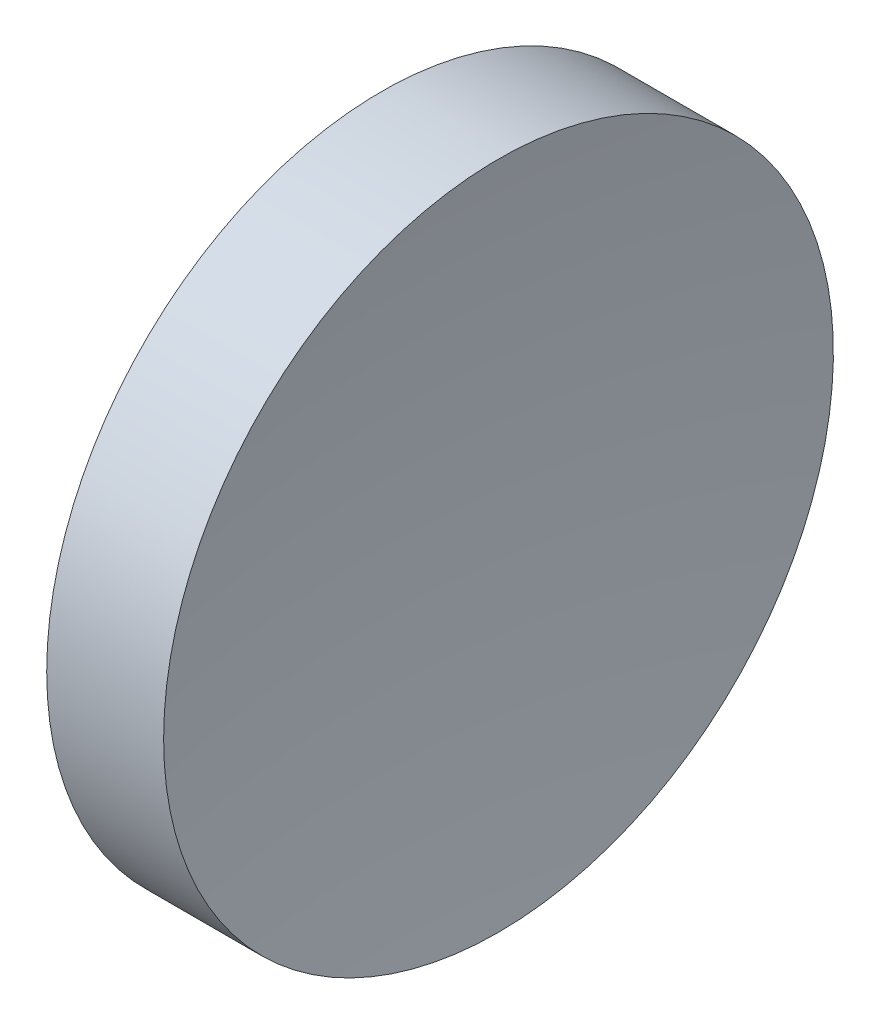
SolidWorks part; units mm, degrees
ref_plane "前视基准面" through (0, 0, 0) normal (0, 0, 1) x (1, 0, 0)
ref_plane "上视基准面" through (0, 0, 0) normal (0, 1, 0) x (1, 0, 0)
ref_plane "右视基准面" through (0, 0, 0) normal (1, 0, 0) x (0, 0, -1)
sketch "草图1" plane through (0, 0, 0) normal (0, 0, 1) x (1, 0, 0)
  line L0 (111.9552, 71.194) -> (137.836, 71.194) construction
  line L1 (119.5068, 71.194) -> (119.5068, 83.894)
  line L2 (119.5068, 83.894) -> (123.941, 83.894)
  line L3 (123.0068, 71.194) -> (119.5068, 71.194)
  arc A0 (123.941, 83.894) -> (123.0068, 71.194) centre (209.8068, 71.194) ccw
revolve "旋转1" add sketch "草图1" angle 360 about L0
